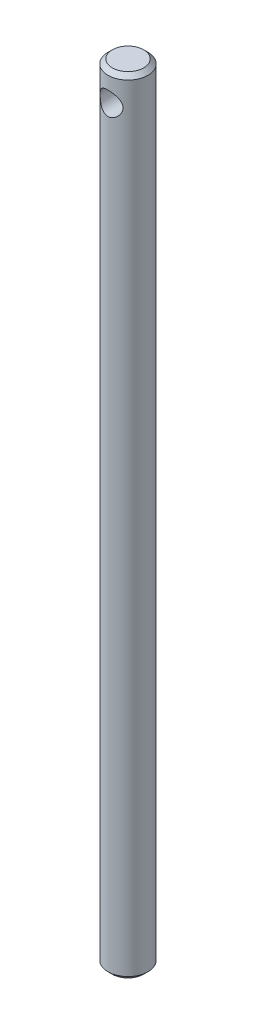
SolidWorks part; units mm, degrees
ref_plane "Front" through (0, 0, 0) normal (0, 0, 1) x (1, 0, 0)
ref_plane "Top" through (0, 0, 0) normal (0, 1, 0) x (1, 0, 0)
ref_plane "Right" through (0, 0, 0) normal (1, 0, 0) x (0, 0, -1)
sketch "Sketch1" plane through (0, 0, 0) normal (0, 1, 0) x (1, 0, 0)
  circle A0 centre (0, 0) radius 14
  dimension "D1" = 28
extrude "Boss-Extrude1" add sketch "Sketch1" along normal blind 550
sketch "Sketch2" plane through (0, 0, 0) normal (0, 0, 1) x (1, 0, 0)
  line L0 (14, 550) -> (-14, 550) construction
  circle A0 centre (0, 530) radius 8
  dimension "D1" = 16
  dimension "D2" = 20
extrude "Cut-Extrude1" cut sketch "Sketch2" against normal through all both and the other way through all
chamfer "Chamfer1" distance 3 angle 45 2 edges at (0, 0, 14) (0, 550, 14)
